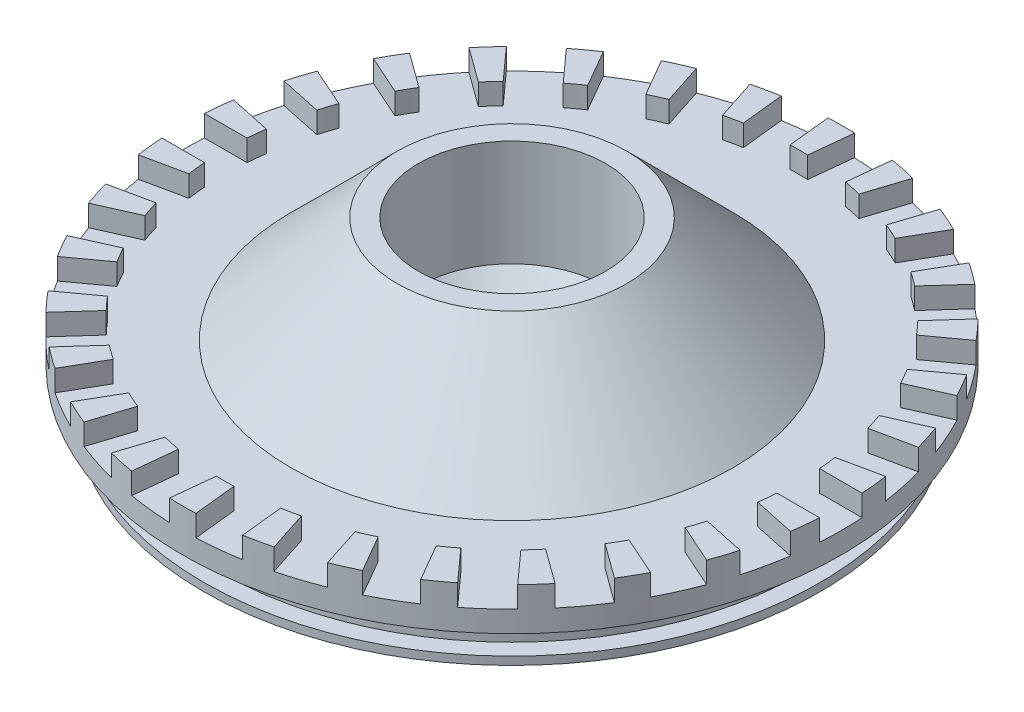
SolidWorks part; units mm, degrees
material "6061-T4 (SS)"
ref_plane "Front Plane" through (0, 0, 0) normal (0, 0, 1) x (1, 0, 0)
ref_plane "Top Plane" through (0, 0, 0) normal (0, 1, 0) x (1, 0, 0)
ref_plane "Right Plane" through (0, 0, 0) normal (1, 0, 0) x (0, 0, -1)
ref_axis "Axis1" through (0, -42.3, 0) along (0, 1, 0)
sketch "Sketch1" plane through (0, 0, 0) normal (0, 0, 1) x (1, 0, 0)
  line L0 (-7.62, 0) -> (-46.0375, 0)
  line L6 (-46.0375, 6.35) -> (-49.2125, 6.35)
  line L20 (-49.2125, 6.35) -> (-49.2125, 12.7)
  line L21 (-42.8625, 9.525) -> (-33.02, 9.525)
  line L22 (-46.0375, 0) -> (-46.0375, 1.2065)
  line L23 (-46.0375, 1.2065) -> (-43.4975, 1.2065)
  line L24 (-43.4975, 1.2065) -> (-43.4975, 4.7625)
  line L25 (-43.4975, 4.7625) -> (-46.0375, 4.7625)
  line L26 (-46.0375, 4.7625) -> (-46.0375, 6.35)
  line L27 (-7.62, 0) -> (-7.62, 3.175)
  line L28 (-7.62, 3.175) -> (-13.97, 9.525)
  line L29 (-13.97, 9.525) -> (-13.97, 25.4)
  line L30 (-13.97, 25.4) -> (-17.145, 25.4)
  line L32 (-7.62, 3.175) -> (-12.2413, 3.175) construction
  line L33 (-49.2125, 12.7) -> (-42.8625, 12.7)
  line L34 (-42.8625, 12.7) -> (-42.8625, 9.525)
  line L35 (-33.02, 9.525) -> (-17.145, 25.4)
  line L36 (-33.02, 9.525) -> (-25.5508, 9.525) construction
  dimension "D2" = 6.35
  dimension "D3" = 1.5875
  dimension "D4" = 2.54
  dimension "D5" = 3.556
  dimension "D6" = 3.175
  dimension "D7" = 3.175
  dimension "D8" = 6.35
  dimension "D9" = 45
  dimension "D10" = 3.175
  dimension "D11" = 3.175
  dimension "D12" = 6.35
  dimension "D13" = 46.0375
  dimension "D14" = 7.62
  dimension "D15" = 6.35
  dimension "D16" = 12.7
  dimension "D17" = 45
revolve "Revolve1" add sketch "Sketch1" angle 360 about axis through (0, -42.3, 0) along (0, 1, 0)
sketch "Sketch2" plane through (0, 12.7, 0) normal (0, 1, 0) x (1, 0, 0)
  line L0 (42.7447, 3.175) -> (55.4447, 3.175)
  line L1 (42.7447, -3.175) -> (55.4447, -3.175)
  line L2 (42.7447, 3.175) -> (42.7447, -3.175)
  line L3 (55.4447, 3.175) -> (55.4447, -3.175)
  circle A0 centre (0, 0) radius 42.8625 construction
  circle A2 centre (0, 0) radius 42.8625 construction
  point P10 (42.7447, 0)
  dimension "D1" = 6.35
  dimension "D2" = 12.7
extrude "Cut-Extrude1" cut sketch "Sketch2" against normal blind 3.175
pattern_circular "CirPattern1" count 30 over 360 about axis through (0, 0, 0) along (0, 1, 0) of "Cut-Extrude1"
